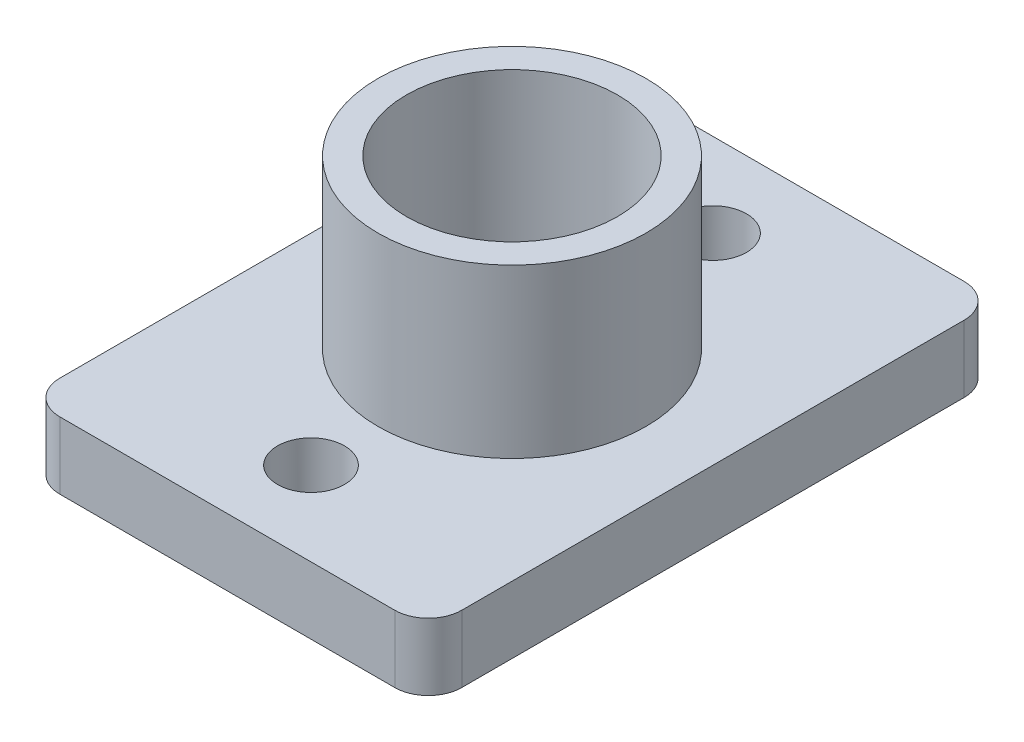
SolidWorks part; units mm, degrees
ref_plane "Front Plane" through (0, 0, 0) normal (0, 0, 1) x (1, 0, 0)
ref_plane "Top Plane" through (0, 0, 0) normal (0, 1, 0) x (1, 0, 0)
ref_plane "Right Plane" through (0, 0, 0) normal (1, 0, 0) x (0, 0, -1)
sketch "Sketch1" plane through (0, 0, 0) normal (0, 1, 0) x (1, 0, 0)
  line L1 (0, 0) -> (12, 0)
  line L2 (0, 0) -> (0, 17)
  line L3 (0, 17) -> (12, 17)
  line L4 (12, 0) -> (12, 17)
  dimension "D1" = 12
  dimension "D2" = 17
extrude "main_body" add sketch "Sketch1" along normal blind 2
sketch "Sketch2" plane through (0, 2, 0) normal (0, 1, 0) x (1, 0, 0)
  line L0 (0, 17) -> (0, 0) construction
  line L1 (0, 0) -> (12, 0) construction
  circle A0 centre (6, 8.5) radius 4
  dimension "D1" = 8
  dimension "D2" = 6
  dimension "D3" = 8.5
extrude "spacer_mount" add sketch "Sketch2" along normal blind 5
sketch "Sketch3" plane through (0, 7, 0) normal (0, 1, 0) x (1, 0, 0)
  line L1 (0, 17) -> (0, 0) construction
  circle A0 centre (6, 8.5) radius 3.15
  circle A1 centre (6, 8.5) radius 4 construction
  circle A2 centre (6, 14.5) radius 1
  circle A3 centre (6, 2.5) radius 1
  dimension "D1" = 0
  dimension "D2" = 6.3
  dimension "D3" = 2
  dimension "D4" = 2
  dimension "D5" = 6
  dimension "D6" = 6
  dimension "D7" = 12
  dimension "D8" = 6
extrude "bolt_spacer_holes" cut sketch "Sketch3" against normal through all
fillet "Fillet1" radius 1 4 edges at (0, 1, -17) (12, 1, -17) (12, 1, 0) (0, 1, 0)
